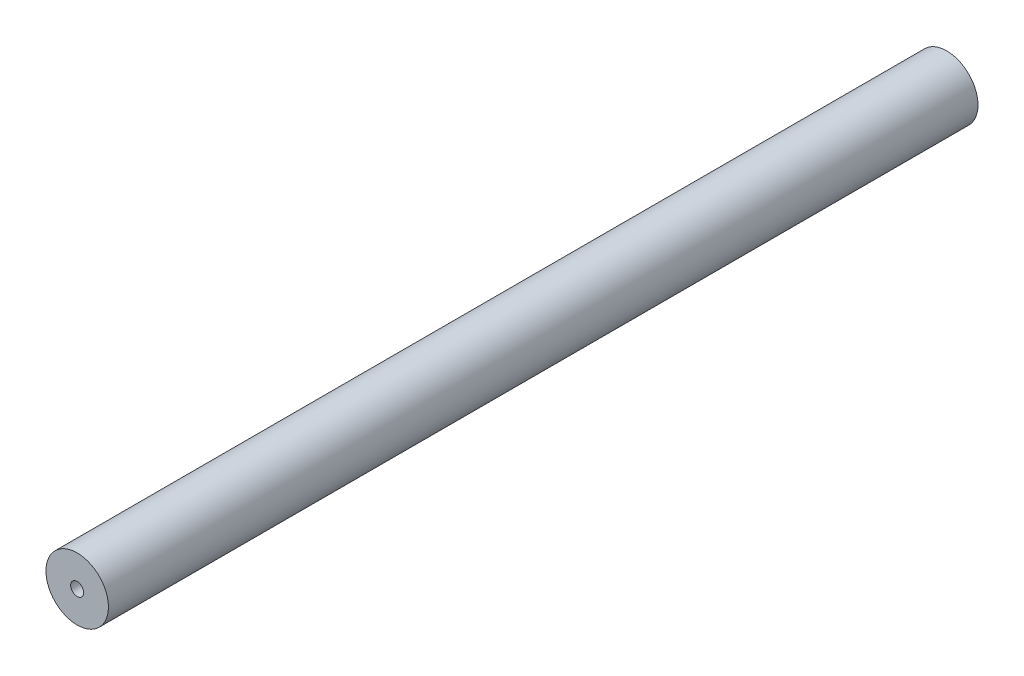
SolidWorks part; units mm, degrees
material "1023 Carbon Steel Sheet (SS)"
ref_plane "Front Plane" through (0, 0, 0) normal (0, 0, 1) x (1, 0, 0)
ref_plane "Top Plane" through (0, 0, 0) normal (0, 1, 0) x (1, 0, 0)
ref_plane "Right Plane" through (0, 0, 0) normal (1, 0, 0) x (0, 0, -1)
sketch "Sketch2" plane through (0, 0, 0) normal (0, 0, 1) x (1, 0, 0)
  circle A0 centre (0, 0) radius 6
  dimension "D1" = 12
extrude "Boss-Extrude1" add sketch "Sketch2" along normal mid plane 167
hole_wizard "Tap Drill for M3x0.5 Tap1" positions "Sketch3" profile "Sketch4" hole size "M3x0.5" standard "ANSI Metric"
sketch "Sketch3" plane through (0, 0, 83.5) normal (0, 0, 1) x (1, 0, 0)
  point P0 (0, 0)
sketch "Sketch4" plane through (0, 0, 83.5) normal (1, 0, 0) x (0, -1, 0)
  line L0 (0, 0) -> (0, 10.7511)
  line L1 (0, 10.7511) -> (1.25, 10)
  line L2 (1.25, 10) -> (1.25, 0)
  line L5 (1.25, 0) -> (0, 0)
  line L10 (0, 10.7511) -> (-1.25, 10) construction
  line L11 (0, -6.35) -> (0, 107.95) construction
  dimension "Hole Dia." = 2.5
  dimension "Hole Depth" = 10
  dimension "Drill Angle" = 118
mirror "Mirror1" about plane through (0, 0, 0) normal (0, 0, 1) of "Tap Drill for M3x0.5 Tap1"
equation "\"tubeOutDiameter\" = 35mm"
equation "\"wheelShaftDiameter\"= 12mm"
equation "\"wheelThickness\"= 135mm"
equation "\"BearingDiameter\"= 20mm"
equation "\"BearingThickness\"= 10mm"
equation "\"frontShaftDiameter\"= 20mm"
equation "\"D1@Sketch2\"=\"wheelShaftDiameter\""
